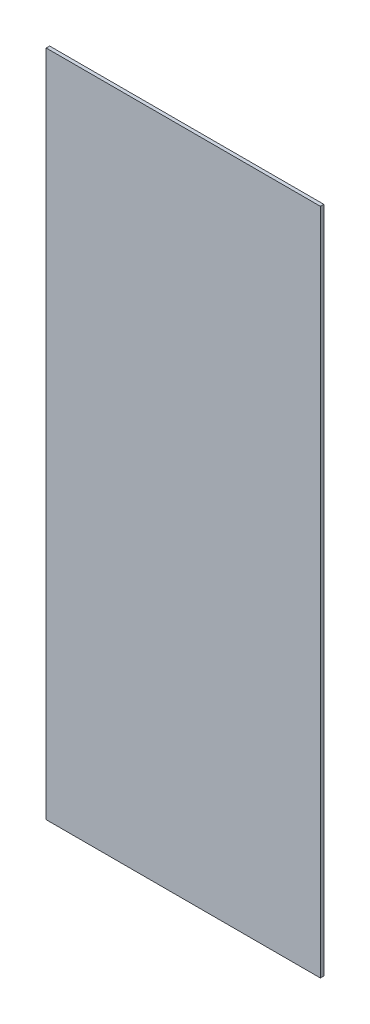
SolidWorks part; units mm, degrees
ref_plane "Front Plane" through (0, 0, 0) normal (0, 0, 1) x (1, 0, 0)
ref_plane "Top Plane" through (0, 0, 0) normal (0, 1, 0) x (1, 0, 0)
ref_plane "Right Plane" through (0, 0, 0) normal (1, 0, 0) x (0, 0, -1)
sketch "Sketch1" plane through (0, 0, 0) normal (0, 0, 1) x (1, 0, 0)
  line L1 (305.6657, -132.3727) -> (385.2516, -132.3727)
  line L2 (305.6657, -132.3727) -> (305.6657, 61.6273)
  line L3 (305.6657, 61.6273) -> (385.2516, 61.6273)
  line L4 (385.2516, -132.3727) -> (385.2516, 61.6273)
extrude "Boss-Extrude1" add sketch "Sketch1" along normal blind 1
